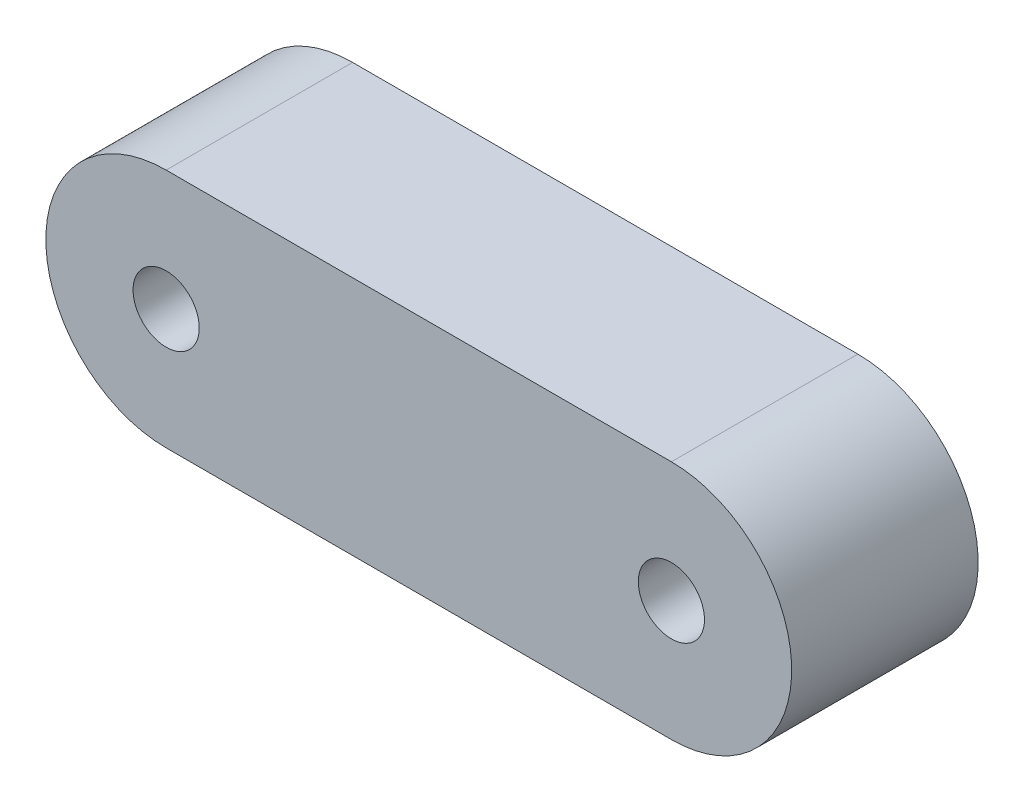
SolidWorks part; units mm, degrees
ref_plane "Front Plane" through (0, 0, 0) normal (0, 0, 1) x (1, 0, 0)
ref_plane "Top Plane" through (0, 0, 0) normal (0, 1, 0) x (1, 0, 0)
ref_plane "Right Plane" through (0, 0, 0) normal (1, 0, 0) x (0, 0, -1)
sketch "Sketch1" plane through (0, 0, 0) normal (0, 0, 1) x (1, 0, 0)
  line L0 (0, 0) -> (-42, 0) construction
  line L1 (0, -10) -> (-42, -10)
  line L2 (0, 10) -> (-42, 10)
  arc A0 (0, -10) -> (0, 10) centre (0, 0) ccw
  arc A1 (-42, 10) -> (-42, -10) centre (-42, 0) ccw
  circle A2 centre (-42, 0) radius 2.75
  circle A3 centre (0, 0) radius 2.75
  point P3 (-21, 0)
  dimension "D3" = 5.5
  dimension "D4" = 5.5
  dimension "D1" = 42
  dimension "D2" = 20
extrude "Boss-Extrude1" add sketch "Sketch1" along normal blind 15.5
